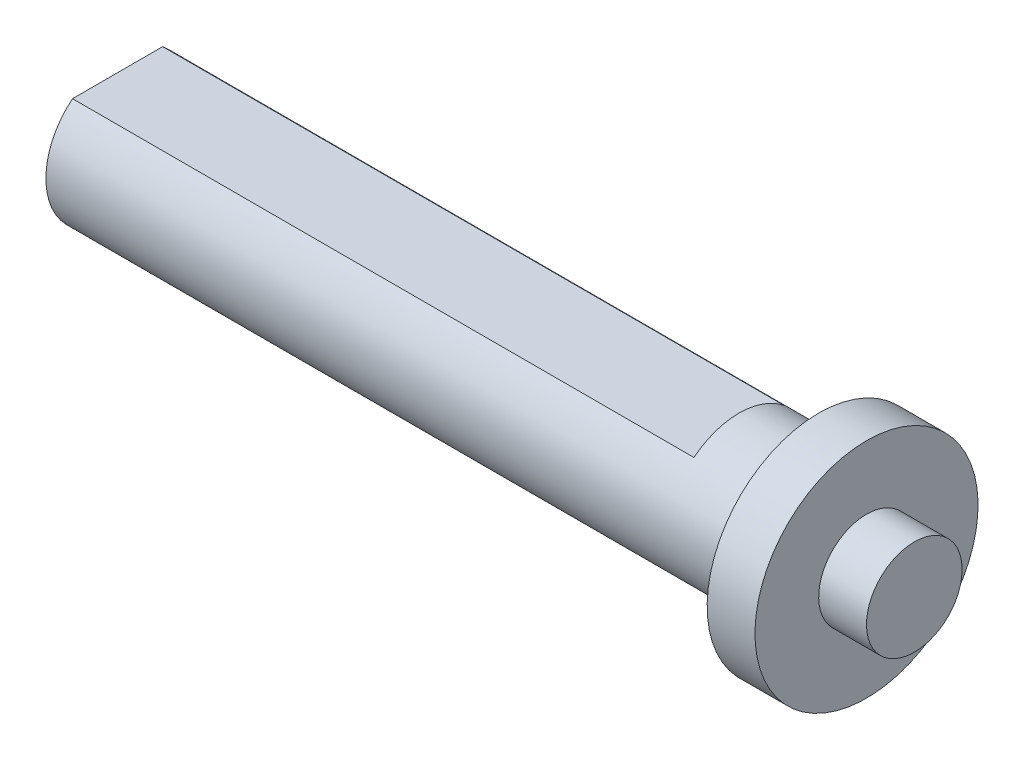
SolidWorks part; units mm, degrees
ref_plane "前基準面" through (0, 0, 0) normal (0, 0, 1) x (1, 0, 0)
ref_plane "上基準面" through (0, 0, 0) normal (0, 1, 0) x (1, 0, 0)
ref_plane "右基準面" through (0, 0, 0) normal (1, 0, 0) x (0, 0, -1)
sketch "草圖1" plane through (0, 0, 0) normal (0, 0, 1) x (1, 0, 0)
  line L0 (0, 7) -> (3, 7)
  line L1 (0, 0) -> (3, 0)
  line L2 (0, 0) -> (0, 7)
  line L4 (3, 0) -> (3, 7)
  line L5 (0, 0) -> (-44, 0)
  line L6 (0, 0) -> (0, 4.5)
  line L7 (0, 4.5) -> (-44, 4.5)
  line L8 (-44, 0) -> (-44, 4.5)
  line L9 (3, 0) -> (6, 0)
  line L10 (3, 0) -> (3, 3)
  line L11 (3, 3) -> (6, 3)
  line L12 (6, 0) -> (6, 3)
  dimension "D1" = 50
  dimension "D2" = 3
  dimension "D3" = 3
  dimension "D4" = 4.5
  dimension "D5" = 7
  dimension "D6" = 3
revolve "旋轉1" add sketch "草圖1" angle 360 about L5
cosmetic thread "裝飾螺紋線2" parameters "D1"=5, "D2"=6.891
sketch "草圖5" plane through (0, 0, 0) normal (0, 0, 1) x (1, 0, 0)
  line L0 (-44, 4.5) -> (-44, -4.5) construction
  line L1 (0, 4.5) -> (-44, 4.5) construction
  line L2 (-44, -4.5) -> (0, -4.5) construction
  line L3 (0, 4.5) -> (0, -4.5) construction
  line L4 (-44, 4.5) -> (-44, -4.5)
  line L5 (0, 4.5) -> (-44, 4.5)
  line L6 (-44, -4.5) -> (0, -4.5)
  line L7 (0, 4.5) -> (0, -4.5)
  line L8 (-44, 3.5) -> (0, 3.5)
  line L9 (-5, 4.5) -> (-5, -4.5)
  line L10 (-44, -3.5) -> (-5, -3.5)
  dimension "D1" = 1
  dimension "D2" = 5
  dimension "D3" = 1
extrude "除料-伸長2" cut sketch "草圖5" against normal mid plane 10 contours L9 L5 L4 L8 | L10 L4 L6 L9
